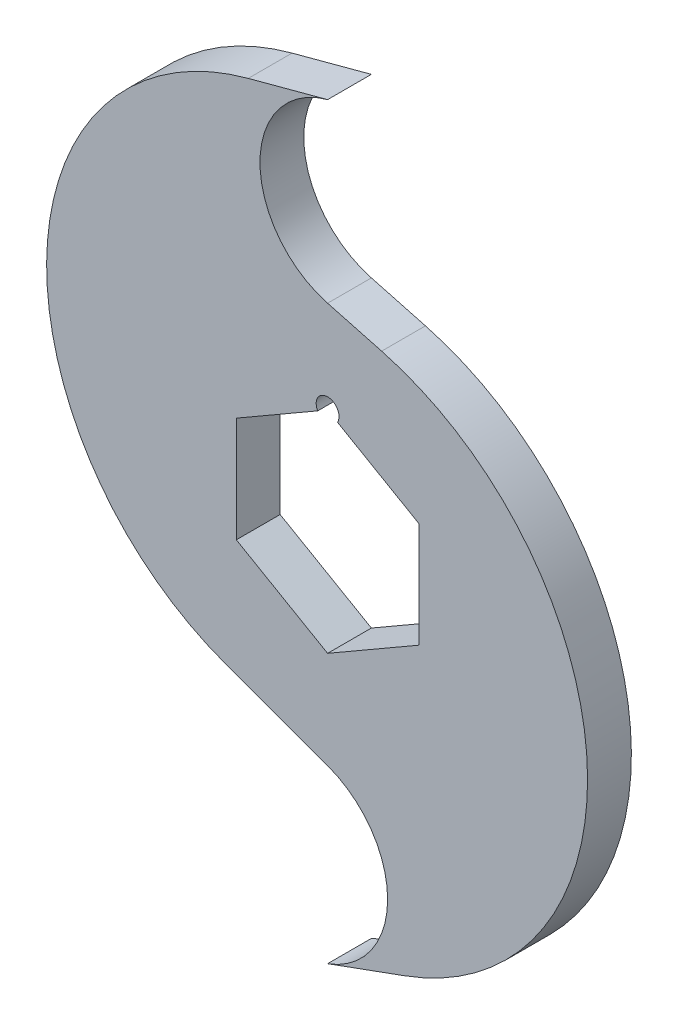
SolidWorks part; units mm, degrees
ref_plane "Front Plane" through (0, 0, 0) normal (0, 0, 1) x (1, 0, 0)
ref_plane "Top Plane" through (0, 0, 0) normal (0, 1, 0) x (1, 0, 0)
ref_plane "Right Plane" through (0, 0, 0) normal (1, 0, 0) x (0, 0, -1)
sketch "Sketch1" plane through (0, 0, 0) normal (0, 0, 1) x (1, 0, 0)
  line L0 (0, 52.07) -> (-11.0405, 49.1117)
  line L1 (0, 52.07) -> (0, 0) construction
  line L2 (0, -52.07) -> (10.7407, -48.1607)
  line L3 (0, 0) -> (0, -52.07) construction
  line L5 (0, 14.6647) -> (-12.7, 7.3323)
  line L6 (-12.7, 7.3323) -> (-12.7, -7.3323)
  line L7 (-12.7, -7.3323) -> (0, -14.6647)
  line L8 (0, -14.6647) -> (12.7, -7.3323)
  line L9 (12.7, -7.3323) -> (12.7, 7.3323)
  line L10 (12.7, 7.3323) -> (0, 14.6647)
  line L11 (0, 27.5355) -> (7.5237, 25.5195)
  line L12 (0, -28.2018) -> (-14.1906, -23.0368)
  circle A0 centre (0, 0) radius 52.07 construction
  arc A1 (0, 52.07) -> (0, 27.5355) centre (3.287, 39.8027) ccw
  arc A3 (0, -52.07) -> (0, -28.2018) centre (-4.3437, -40.1359) ccw
  arc A4 (10.7407, -48.1607) -> (7.5237, 25.5195) centre (-2.4834, -11.8278) ccw
  arc A5 (-11.0405, 49.1117) -> (-14.1906, -23.0368) centre (-1.2414, 12.5408) ccw
  circle A6 centre (0, 0) radius 12.7 construction
  circle A7 centre (0, 14.6647) radius 1.5875
  dimension "D4" = 70
  dimension "D5" = 25.4
  dimension "D1" = 104.14
  dimension "D6" = 12.7
  dimension "D7" = 3.175
  dimension "D2" = 11.43
  dimension "D3" = 75
extrude "Boss-Extrude1" add sketch "Sketch1" along normal mid plane 6.096 contours L0 A5 L12 A3 L2 A4 L11 A1 A7 L10 L9 L8 L7 L6 L5
